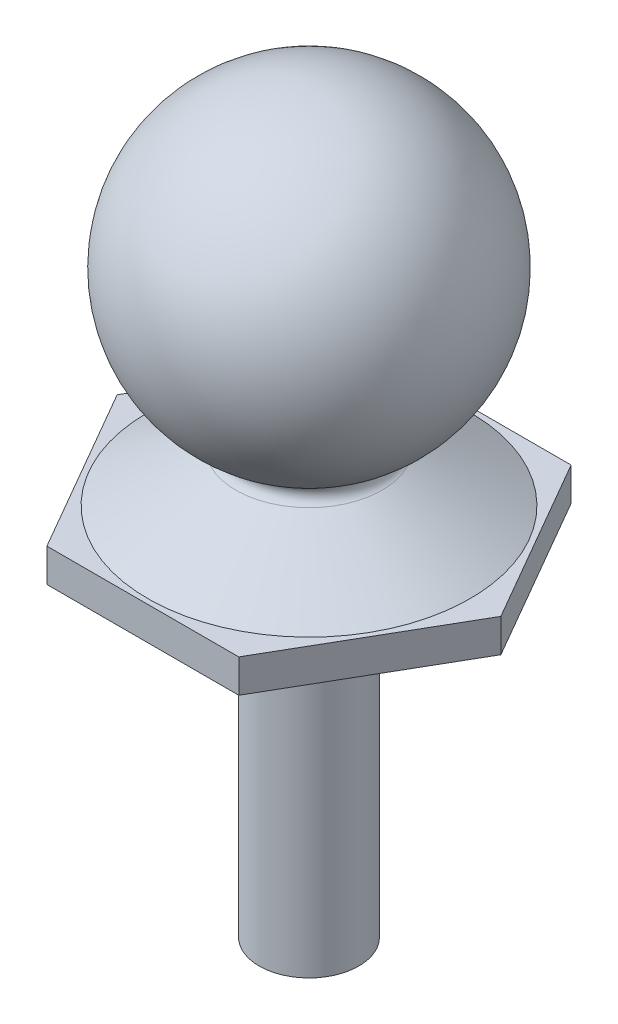
SolidWorks part; units mm, degrees
ref_plane "Front Plane" through (0, 0, 0) normal (0, 0, 1) x (1, 0, 0)
ref_plane "Top Plane" through (0, 0, 0) normal (0, 1, 0) x (1, 0, 0)
ref_plane "Right Plane" through (0, 0, 0) normal (1, 0, 0) x (0, 0, -1)
sketch "Sketch1" plane through (0, 0, 0) normal (0, 0, 1) x (1, 0, 0)
  line L0 (0, 0) -> (0, -4.7096) construction
  line L8 (2.2, -4.7096) -> (4.85, -6.2096)
  line L9 (4.85, -6.2096) -> (5, -6.2096)
  line L10 (5, -6.2096) -> (5, -7.2096)
  line L14 (1.5, -7.2096) -> (1.5, -17.4596)
  line L17 (1.5, -7.2096) -> (5, -7.2096)
  line L18 (0, 4.7096) -> (0, -17.4596)
  line L19 (0, -17.4596) -> (1.5, -17.4596)
  arc A0 (2.2, -4.1642) -> (0, 4.7096) centre (0, 0) ccw
  arc A1 (2.2, -4.7096) -> (2.2, -4.1642) centre (2.3544, -4.4369) cw
  dimension "D1" = 4.7096
  dimension "D3" = 10.25
  dimension "D4" = 0.3134
  dimension "D2" = 1.5
  dimension "D5" = 1
  dimension "D6" = 22.1692
  dimension "D8" = 3.5
revolve "Revolve1" add sketch "Sketch1" angle 360 about L18
sketch "Sketch3" plane through (0, -7.2096, 0) normal (0, -1, 0) x (1, 0, 0)
  line L1 (5.7735, 0) -> (2.8868, 5)
  line L2 (2.8868, 5) -> (-2.8868, 5)
  line L3 (-2.8868, 5) -> (-5.7735, 0)
  line L4 (-5.7735, 0) -> (-2.8868, -5)
  line L5 (-2.8868, -5) -> (2.8868, -5)
  line L6 (2.8868, -5) -> (5.7735, 0)
  circle A0 centre (0, 0) radius 5 construction
  dimension "D1" = 10
extrude "Boss-Extrude1" add sketch "Sketch3" against normal blind 1
